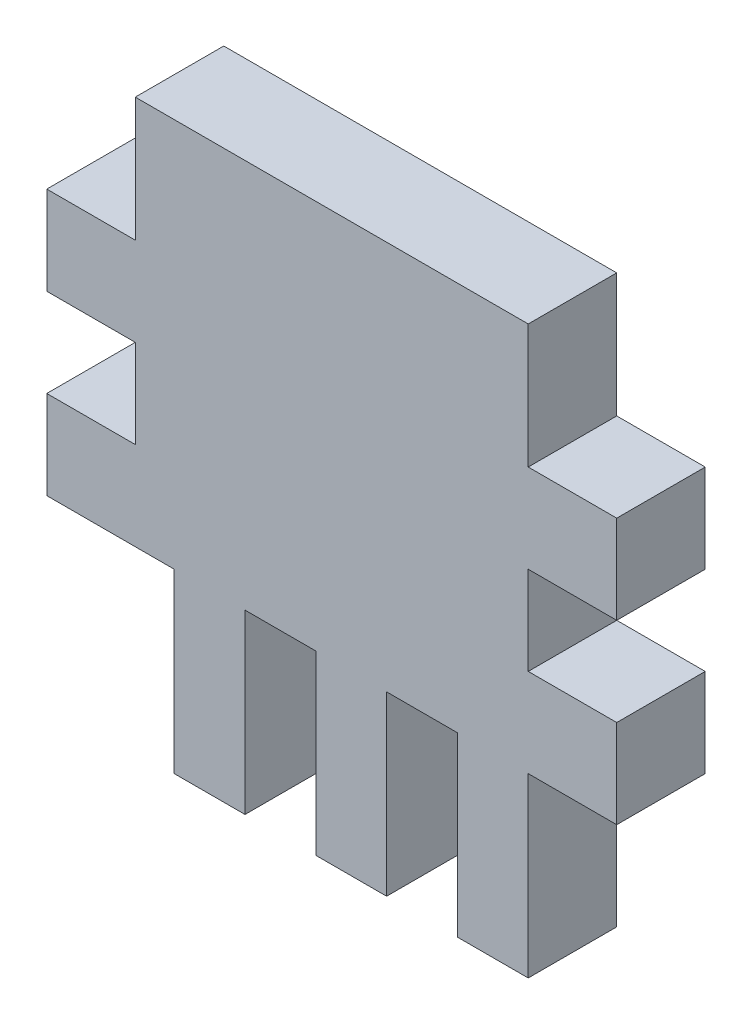
SolidWorks part; units mm, degrees
ref_plane "Plan de face" through (0, 0, 0) normal (0, 0, 1) x (1, 0, 0)
ref_plane "Plan de dessus" through (0, 0, 0) normal (0, 1, 0) x (1, 0, 0)
ref_plane "Plan de droite" through (0, 0, 0) normal (1, 0, 0) x (0, 0, -1)
sketch "Esquisse2" plane through (0, 0, 0) normal (0, 0, 1) x (1, 0, 0)
  line L0 (27.5058, 0) -> (27.5058, 16) construction
  line L1 (1.3605, -1.2131) -> (23.5605, -1.2131)
  line L2 (1.3605, -1.2131) -> (1.3605, 20.7869)
  line L3 (1.3605, 20.7869) -> (23.5605, 20.7869)
  line L4 (23.5605, -1.2131) -> (23.5605, 20.7869)
  line L5 (27.5058, 16) -> (-10.8221, 16) construction
  line L11 (3.5605, -1.2131) -> (7.5605, -1.2131)
  line L12 (3.5605, -1.2131) -> (3.5605, -11.2131)
  line L13 (3.5605, -11.2131) -> (7.5605, -11.2131)
  line L14 (7.5605, -1.2131) -> (7.5605, -11.2131)
  line L15 (23.5605, -1.2131) -> (28.5605, -1.2131)
  line L16 (23.5605, -1.2131) -> (23.5605, 3.7869)
  line L17 (23.5605, 3.7869) -> (28.5605, 3.7869)
  line L18 (28.5605, -1.2131) -> (28.5605, 3.7869)
  line L19 (23.5605, 8.7869) -> (28.5605, 8.7869)
  line L20 (23.5605, 8.7869) -> (23.5605, 13.7869)
  line L21 (23.5605, 13.7869) -> (28.5605, 13.7869)
  line L22 (28.5605, 8.7869) -> (28.5605, 13.7869)
  line L23 (1.3605, -1.2131) -> (-3.6395, -1.2131)
  line L24 (1.3605, -1.2131) -> (1.3605, 3.7869)
  line L25 (1.3605, 3.7869) -> (-3.6395, 3.7869)
  line L26 (-3.6395, -1.2131) -> (-3.6395, 3.7869)
  line L27 (11.5605, -1.2131) -> (15.5605, -1.2131)
  line L28 (11.5605, -1.2131) -> (11.5605, -11.2131)
  line L29 (11.5605, -11.2131) -> (15.5605, -11.2131)
  line L30 (15.5605, -1.2131) -> (15.5605, -11.2131)
  line L31 (23.5605, -1.2131) -> (19.5605, -1.2131)
  line L32 (23.5605, -1.2131) -> (23.5605, -11.2131)
  line L33 (23.5605, -11.2131) -> (19.5605, -11.2131)
  line L34 (19.5605, -1.2131) -> (19.5605, -11.2131)
  line L35 (1.3605, 8.7869) -> (-3.6395, 8.7869)
  line L36 (1.3605, 8.7869) -> (1.3605, 13.7869)
  line L37 (1.3605, 13.7869) -> (-3.6395, 13.7869)
  line L38 (-3.6395, 8.7869) -> (-3.6395, 13.7869)
  dimension "D1" = 22.2
  dimension "D2" = 22
  dimension "D3" = 16
  dimension "D4" = 5
  dimension "D5" = 5
  dimension "D6" = 5
  dimension "D7" = 10
  dimension "D8" = 5
  dimension "D9" = 5
  dimension "D11" = 4
  dimension "D12" = 10
  dimension "D13" = 4
  dimension "D14" = 4
  dimension "D15" = 10
  dimension "D16" = 90
  dimension "D17" = 4
  dimension "D18" = 4
  dimension "D19" = 5
  dimension "D20" = 5
  dimension "D21" = 5
  dimension "D22" = 5
extrude "Boss.-Extru.1" add sketch "Esquisse2" along normal blind 5
